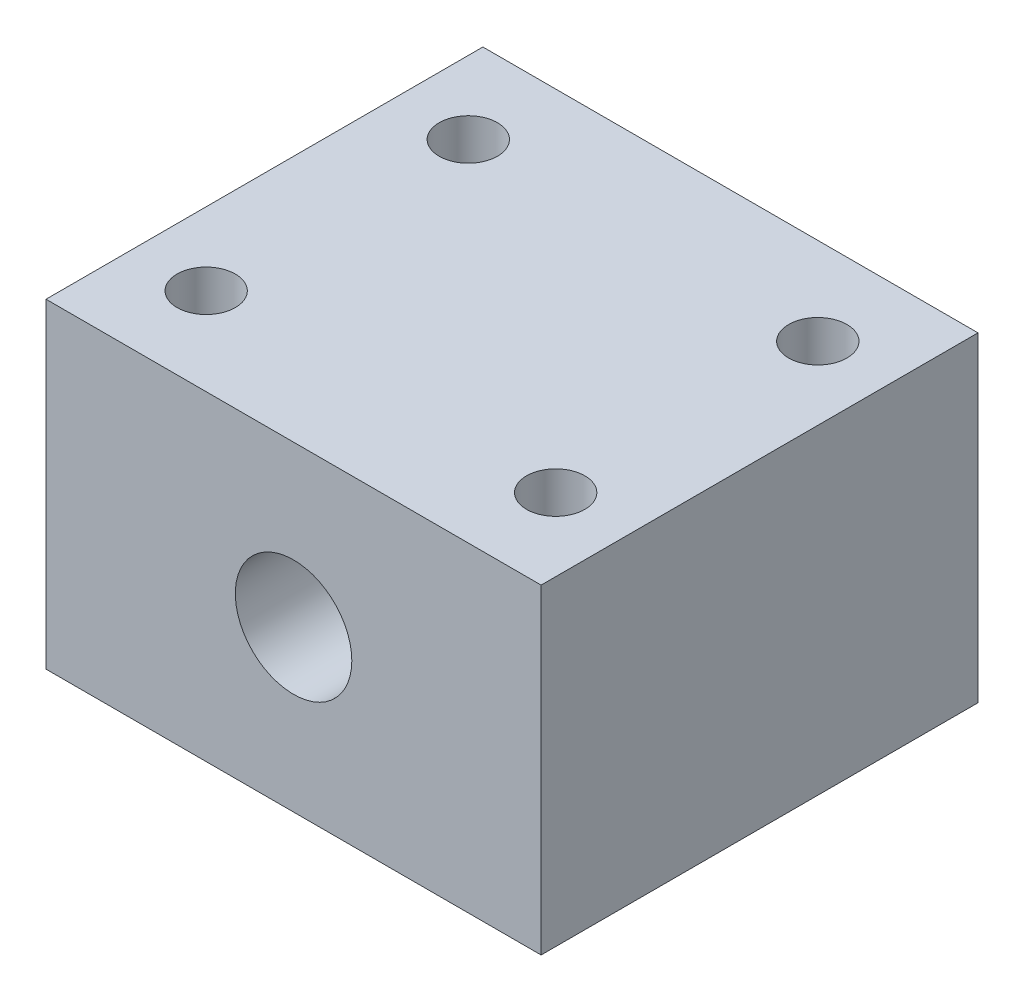
SolidWorks part; units mm, degrees
ref_plane "Front Plane" through (0, 0, 0) normal (0, 0, 1) x (1, 0, 0)
ref_plane "Top Plane" through (0, 0, 0) normal (0, 1, 0) x (1, 0, 0)
ref_plane "Right Plane" through (0, 0, 0) normal (1, 0, 0) x (0, 0, -1)
sketch "Sketch1" plane through (0, 0, 0) normal (0, 0, 1) x (1, 0, 0)
  line L0 (17, 22) -> (17, 0) construction
  line L1 (0, 0) -> (34, 0)
  line L2 (0, 0) -> (0, 22)
  line L3 (0, 22) -> (34, 22)
  line L4 (34, 0) -> (34, 22)
  circle A0 centre (17, 11) radius 4
  dimension "D4" = 8
  dimension "D1" = 34
  dimension "D2" = 22
  dimension "D3" = 11
extrude "Boss-Extrude1" add sketch "Sketch1" along normal blind 30
sketch "Sketch2" plane through (0, 22, 0) normal (0, 1, 0) x (1, 0, 0)
  line L0 (17, 0) -> (17, -30) construction
  line L1 (34, 0) -> (0, 0) construction
  line L2 (34, -30) -> (0, -30) construction
  line L3 (0, -15) -> (34, -15) construction
  line L4 (0, -30) -> (0, 0) construction
  line L5 (34, -30) -> (34, 0) construction
  circle A0 centre (5, -24) radius 2
  circle A1 centre (5, -6) radius 2
  circle A2 centre (29, -6) radius 2
  circle A3 centre (29, -24) radius 2
  dimension "D1" = 4
  dimension "D2" = 24
  dimension "D3" = 12
  dimension "D4" = 18
  dimension "D5" = 9
extrude "Cut-Extrude1" cut sketch "Sketch2" against normal through all
